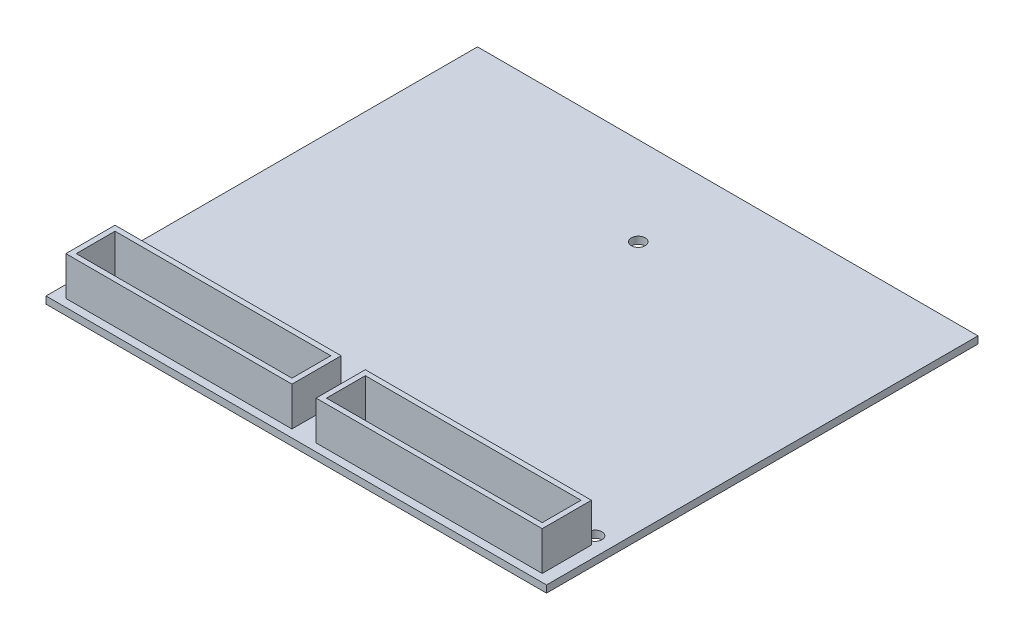
SolidWorks part; units mm, degrees
ref_plane "Front Plane" through (0, 0, 0) normal (0, 0, 1) x (1, 0, 0)
ref_plane "Top Plane" through (0, 0, 0) normal (0, 1, 0) x (1, 0, 0)
ref_plane "Right Plane" through (0, 0, 0) normal (1, 0, 0) x (0, 0, -1)
sketch "Sketch1" plane through (0, 0, 0) normal (0, 1, 0) x (1, 0, 0)
  line L1 (0, 0) -> (116, 0)
  line L2 (0, 0) -> (0, 100)
  line L3 (0, 100) -> (116, 100)
  line L4 (116, 0) -> (116, 100)
  dimension "D1" = 100
  dimension "D2" = 116
extrude "Boss-Extrude1" add sketch "Sketch1" along normal blind 1.65
hole_wizard "M3 Clearance Hole1" positions "Sketch3" profile "Sketch4" hole size "M3" standard "ISO"
sketch "Sketch3" plane through (0, 1.65, 0) normal (0, 1, 0) x (1, 0, 0)
  line L1 (0, 0) -> (116, 0) construction
  line L2 (0, 100) -> (0, 0) construction
  point P0 (4, 15.5)
  point P2 (111.75, 15.5)
  point P4 (57.75, 79.5)
  dimension "D1" = 15.5
  dimension "D2" = 4
  dimension "D3" = 4.25
  dimension "D4" = 79.5
  dimension "D5" = 57.75
sketch "Sketch4" plane through (4, 1.65, -15.5) normal (1, 0, 0) x (0, 0, 1)
  line L0 (0, 0) -> (0, 20.9614)
  line L1 (0, 20.9614) -> (1.6, 20)
  line L2 (1.6, 20) -> (1.6, 0)
  line L5 (1.6, 0) -> (0, 0)
  line L10 (0, 20.9614) -> (-1.6, 20) construction
  line L11 (0, -6.35) -> (0, 107.95) construction
  dimension "Hole Dia." = 3.2
  dimension "Hole Depth" = 20
  dimension "Drill Angle" = 118
sketch "Sketch5" plane through (0, 1.65, 0) normal (0, 1, 0) x (1, 0, 0)
  line L0 (18.9009, 33.5525) -> (18.9009, 45.5326) construction
  line L1 (26.314, 89.1131) -> (38.1144, 89.1131) construction
  line L2 (18.9009, 62.2337) -> (18.9009, 83.1332) construction
  line L3 (47.1389, 89.1131) -> (59.8607, 89.1131) construction
  line L4 (85.8921, 89.1131) -> (105.7937, 89.1131) construction
  line L5 (109.0058, 80.1672) -> (109.0058, 48.6105) construction
  line L6 (109.0058, 41.0178) -> (109.0058, 27.7175) construction
  text T0 "Encoder"
  text T1 "IMU"
  text T2 "Motor Driver"
  text T3 "Steering"
  text T4 "GPS"
sketch "Sketch6" plane through (0, 1.65, 0) normal (0, 1, 0) x (1, 0, 0)
  line L0 (116, 0) -> (116, 100) construction
  line L1 (4, 3) -> (54, 3)
  line L2 (4, 3) -> (4, 12)
  line L3 (4, 12) -> (54, 12)
  line L4 (54, 3) -> (54, 12)
  line L5 (62, 3) -> (112, 3)
  line L6 (62, 3) -> (62, 12)
  line L7 (62, 12) -> (112, 12)
  line L8 (112, 3) -> (112, 12)
  line L10 (0, 100) -> (0, 0) construction
  dimension "D1" = 50
  dimension "D2" = 9
  dimension "D3" = 3
  dimension "D4" = 4
  dimension "D5" = 4
extrude "Extrude-Thin1" add sketch "Sketch6" along normal blind 9 thin
